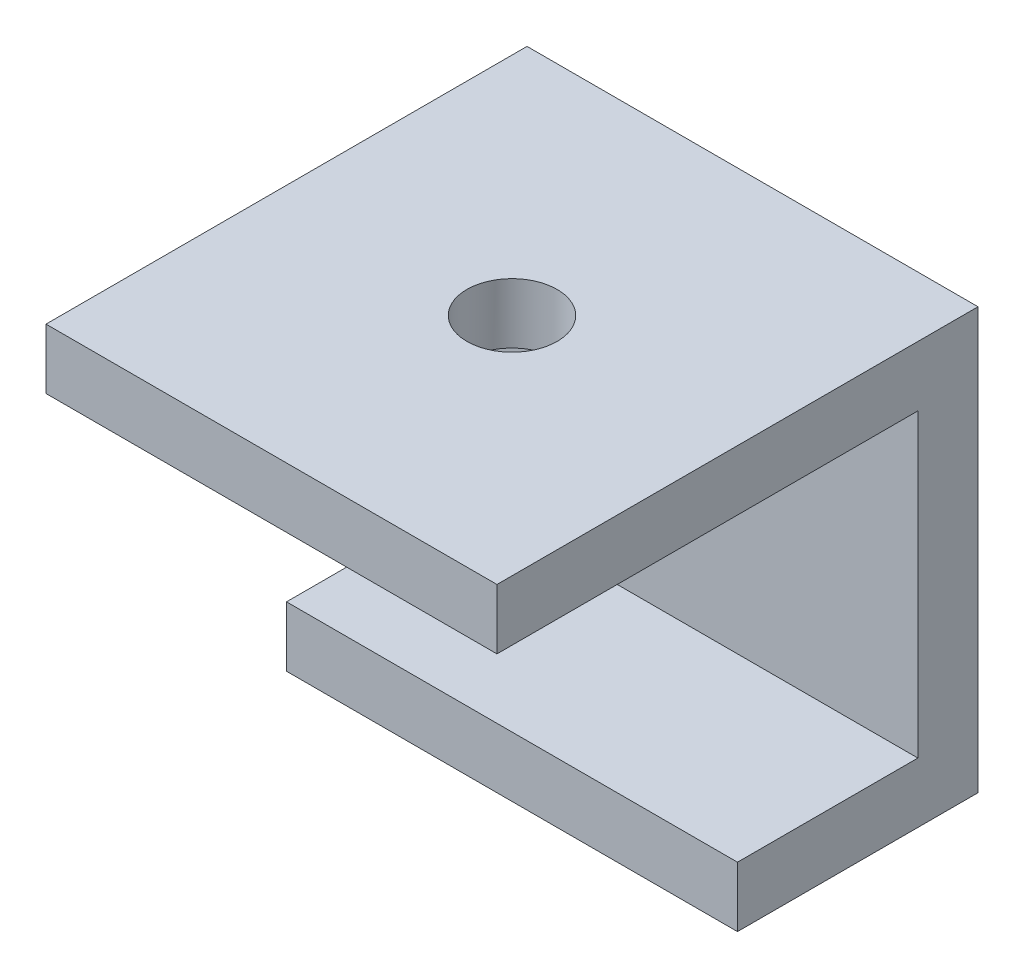
SolidWorks part; units mm, degrees
ref_plane "Front Plane" through (0, 0, 0) normal (0, 0, 1) x (1, 0, 0)
ref_plane "Top Plane" through (0, 0, 0) normal (0, 1, 0) x (1, 0, 0)
ref_plane "Right Plane" through (0, 0, 0) normal (1, 0, 0) x (0, 0, -1)
sketch "Sketch1" plane through (0, 0, 0) normal (1, 0, 0) x (0, 0, -1)
  line L0 (0, 0) -> (0, -14)
  line L1 (0, -14) -> (-8, -14)
  line L2 (-8, -14) -> (-8, -12)
  line L3 (-8, -12) -> (-2, -12)
  line L4 (-2, -12) -> (-2, -2)
  line L5 (-2, -2) -> (-16, -2)
  line L6 (-16, -2) -> (-16, 0)
  line L7 (-16, 0) -> (0, 0)
  dimension "D1" = 2
  dimension "D2" = 16
  dimension "D3" = 14
  dimension "D4" = 2
  dimension "D5" = 2
  dimension "D6" = 8
  dimension "D7" = 6
  dimension "D8" = 14
  dimension "D9" = 10
extrude "Boss-Extrude1" add sketch "Sketch1" against normal blind 15
sketch "Sketch2" plane through (0, 0, 0) normal (0, 1, 0) x (1, 0, 0)
  line L0 (-15, 0) -> (-15, -16) construction
  line L1 (-15, 0) -> (0, 0) construction
  circle A0 centre (-7.5, -8) radius 1.5
  dimension "D3" = 3
  dimension "D1" = 7.5
  dimension "D2" = 8
extrude "Cut-Extrude1" cut sketch "Sketch2" against normal up to next
